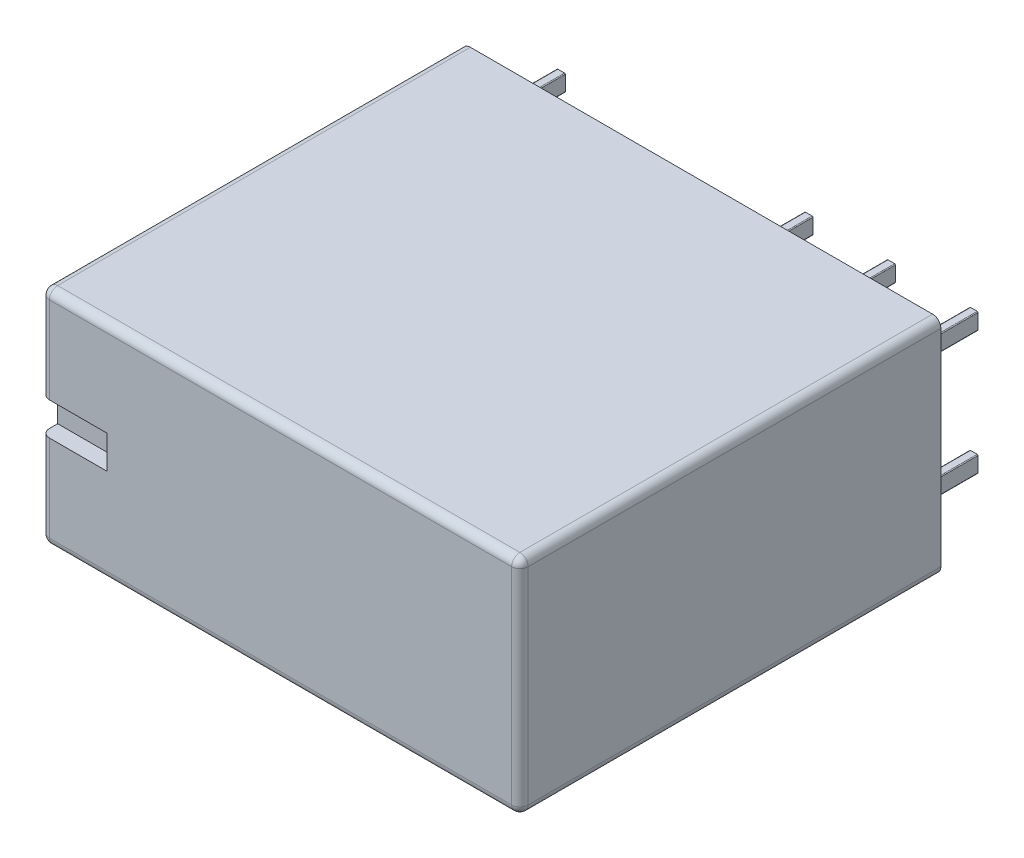
SolidWorks part; units mm, degrees
ref_plane "Спереди" through (0, 0, 0) normal (0, 0, 1) x (1, 0, 0)
ref_plane "Сверху" through (0, 0, 0) normal (0, 1, 0) x (1, 0, 0)
ref_plane "Справа" through (0, 0, 0) normal (1, 0, 0) x (0, 0, -1)
sketch "Эскиз1" plane through (0, 0, 0) normal (0, 0, 1) x (1, 0, 0)
  line L1 (-14.5, 6.75) -> (14.5, 6.75)
  line L2 (-14.5, 6.75) -> (-14.5, -6.75)
  line L3 (-14.5, -6.75) -> (14.5, -6.75)
  line L4 (14.5, 6.75) -> (14.5, -6.75)
  line L5 (-14.5, 6.75) -> (14.5, -6.75) construction
  line L6 (-14.5, -6.75) -> (14.5, 6.75) construction
  point P0 (0, 0)
  dimension "D1" = 13.5
  dimension "D2" = 29
extrude "Бобышка-Вытянуть1" add sketch "Эскиз1" along normal blind 25.5
fillet "Скругление1" radius 0.5 8 edges at (14.5, 6.75, 12.75) (14.5, -6.75, 12.75) (14.5, 0, 25.5) (0, 6.75, 25.5) (0, -6.75, 25.5) (-14.5, 6.75, 12.75) (-14.5, 0, 25.5) (-14.5, -6.75, 12.75)
sketch "Эскиз2" plane through (0, 0, 25.5) normal (0, 0, 1) x (1, 0, 0)
  line L0 (-14.5, -6.25) -> (-14.5, 6.25) construction
  line L1 (-14.5, 1.0021) -> (-10.5, 1.0021)
  line L2 (-14.5, 1.0021) -> (-14.5, -0.9979)
  line L3 (-14.5, -0.9979) -> (-10.5, -0.9979)
  line L4 (-10.5, 1.0021) -> (-10.5, -0.9979)
  line L5 (-10.2957, 0) -> (-14.6688, 0) construction
  dimension "D1" = 2
  dimension "D2" = 4
extrude "Вырез-Вытянуть1" cut sketch "Эскиз2" against normal blind 1
sketch "Эскиз3" plane through (0, 0, 0) normal (0, 0, -1) x (-1, 0, 0)
  line L0 (16.7663, 0) -> (-17.699, 0) construction
  line L1 (12.75, -3.25) -> (12.25, -3.25)
  line L2 (12.75, -3.25) -> (12.75, -4.25)
  line L3 (12.75, -4.25) -> (12.25, -4.25)
  line L4 (12.25, -3.25) -> (12.25, -4.25)
  line L5 (12.75, -3.25) -> (12.25, -4.25) construction
  line L6 (12.75, -4.25) -> (12.25, -3.25) construction
  line L7 (-2.25, -3.25) -> (-2.75, -3.25)
  line L8 (-2.25, -3.25) -> (-2.25, -4.25)
  line L9 (-2.25, -4.25) -> (-2.75, -4.25)
  line L10 (-2.75, -3.25) -> (-2.75, -4.25)
  line L11 (-2.25, -3.25) -> (-2.75, -4.25) construction
  line L12 (-2.25, -4.25) -> (-2.75, -3.25) construction
  line L13 (-7.25, -3.25) -> (-7.75, -3.25)
  line L14 (-7.25, -3.25) -> (-7.25, -4.25)
  line L15 (-7.25, -4.25) -> (-7.75, -4.25)
  line L16 (-7.75, -3.25) -> (-7.75, -4.25)
  line L17 (-7.25, -3.25) -> (-7.75, -4.25) construction
  line L18 (-7.25, -4.25) -> (-7.75, -3.25) construction
  line L19 (-12.25, -3.25) -> (-12.75, -3.25)
  line L20 (-12.25, -3.25) -> (-12.25, -4.25)
  line L21 (-12.25, -4.25) -> (-12.75, -4.25)
  line L22 (-12.75, -3.25) -> (-12.75, -4.25)
  line L23 (-12.25, -3.25) -> (-12.75, -4.25) construction
  line L24 (-12.25, -4.25) -> (-12.75, -3.25) construction
  line L25 (-14.5, -6.25) -> (-14.5, 6.25) construction
  line L27 (-12.25, 4.25) -> (-12.75, 3.25) construction
  line L28 (-12.25, 3.25) -> (-12.75, 4.25) construction
  line L29 (-7.25, 4.25) -> (-7.75, 3.25) construction
  line L30 (-7.25, 3.25) -> (-7.75, 4.25) construction
  line L31 (-2.25, 4.25) -> (-2.75, 3.25) construction
  line L32 (-2.25, 3.25) -> (-2.75, 4.25) construction
  line L33 (12.75, 4.25) -> (12.25, 3.25) construction
  line L34 (12.75, 3.25) -> (12.25, 4.25) construction
  line L35 (-12.75, 3.25) -> (-12.75, 4.25)
  line L36 (-12.25, 4.25) -> (-12.75, 4.25)
  line L37 (-12.25, 3.25) -> (-12.25, 4.25)
  line L38 (-12.25, 3.25) -> (-12.75, 3.25)
  line L39 (-7.75, 3.25) -> (-7.75, 4.25)
  line L40 (-7.25, 4.25) -> (-7.75, 4.25)
  line L41 (-7.25, 3.25) -> (-7.25, 4.25)
  line L42 (-7.25, 3.25) -> (-7.75, 3.25)
  line L43 (-2.75, 3.25) -> (-2.75, 4.25)
  line L44 (-2.25, 4.25) -> (-2.75, 4.25)
  line L45 (-2.25, 3.25) -> (-2.25, 4.25)
  line L46 (-2.25, 3.25) -> (-2.75, 3.25)
  line L47 (12.25, 3.25) -> (12.25, 4.25)
  line L48 (12.75, 4.25) -> (12.25, 4.25)
  line L49 (12.75, 3.25) -> (12.75, 4.25)
  line L50 (12.75, 3.25) -> (12.25, 3.25)
  point P0 (12.5, -3.75)
  point P5 (-2.5, -3.75)
  point P10 (-7.5, -3.75)
  point P15 (-12.5, -3.75)
  point P23 (0, 0)
  point P42 (-12.5, 3.75)
  point P43 (-7.5, 3.75)
  point P44 (-2.5, 3.75)
  point P45 (12.5, 3.75)
  dimension "D1" = 1
  dimension "D2" = 0.5
  dimension "D3" = 20
  dimension "D4" = 5
  dimension "D5" = 5
  dimension "D6" = 2
  dimension "D7" = 3.75
extrude "Бобышка-Вытянуть2" add sketch "Эскиз3" along normal blind 4
fillet "Скругление2" radius 0.05 32 edges at (2.25, -4.25, -2) (2.75, 4.25, -2) (7.25, 4.25, -2) (7.75, 4.25, -2) (12.25, 4.25, -2) (12.75, 4.25, -2) (7.75, -3.25, -2) (12.75, -3.25, -2) (7.75, 3.25, -2) (7.25, 3.25, -2) (12.75, -4.25, -2) (12.25, -4.25, -2) (12.25, -3.25, -2) (12.75, 3.25, -2) (12.25, 3.25, -2) (7.75, -4.25, -2) (7.25, -4.25, -2) (7.25, -3.25, -2) (2.75, -4.25, -2) (2.75, -3.25, -2) (2.25, -3.25, -2) (2.75, 3.25, -2) (2.25, 3.25, -2) (2.25, 4.25, -2) (-12.25, 4.25, -2) (-12.25, -3.25, -2) (-12.75, -3.25, -2) (-12.25, -4.25, -2) (-12.75, -4.25, -2) (-12.75, 4.25, -2) (-12.25, 3.25, -2) (-12.75, 3.25, -2)
